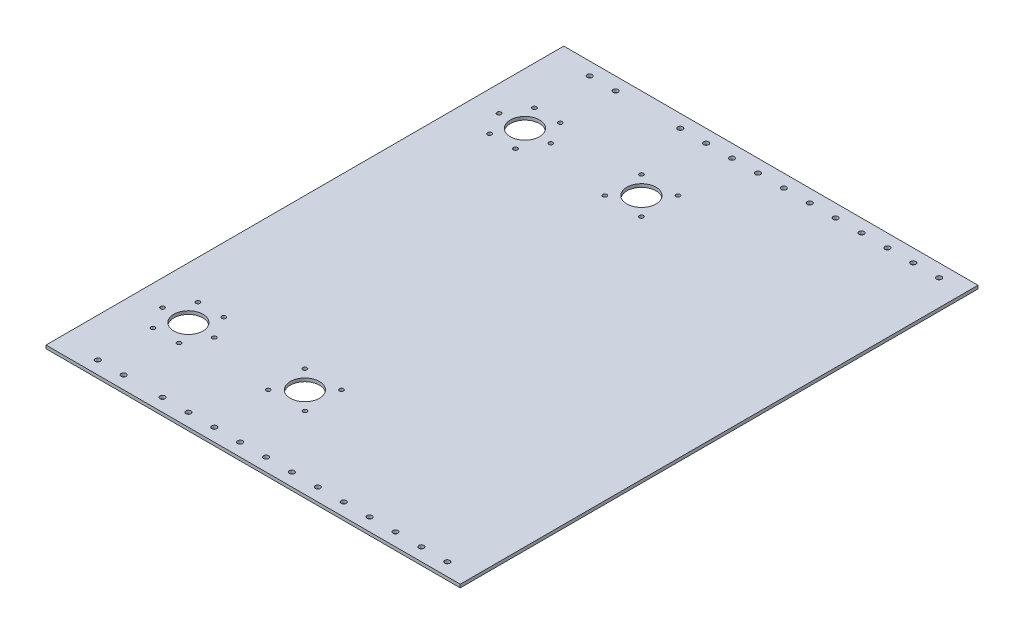
SolidWorks part; units mm, degrees
material "Lexan"
ref_plane "Front Plane" through (0, 0, 0) normal (0, 0, 1) x (1, 0, 0)
ref_plane "Top Plane" through (0, 0, 0) normal (0, 1, 0) x (1, 0, 0)
ref_plane "Right Plane" through (0, 0, 0) normal (1, 0, 0) x (0, 0, -1)
sketch "Sketch1" plane through (0, 0, 0) normal (0, 1, 0) x (1, 0, 0)
  line L1 (0, 0) -> (406.4, 0)
  line L2 (0, 0) -> (0, 508)
  line L3 (0, 508) -> (406.4, 508)
  line L4 (406.4, 0) -> (406.4, 508)
  dimension "D1" = 406.4
  dimension "D2" = 508
extrude "Boss-Extrude1" add sketch "Sketch1" along normal blind 3.175
sketch "Sketch2" plane through (0, 3.175, 0) normal (0, 1, 0) x (1, 0, 0)
  line L0 (107.95, 419.1) -> (107.95, 508) construction
  line L1 (50.8, 419.1) -> (165.1, 419.1) construction
  line L2 (406.4, 0) -> (406.4, 508) construction
  line L3 (50.8, 88.9) -> (165.1, 88.9) construction
  line L5 (406.4, 508) -> (0, 508) construction
  line L6 (107.95, 88.9) -> (107.95, 0) construction
  line L7 (0, 0) -> (406.4, 0) construction
  circle A0 centre (50.8, 419.1) radius 14.2875
  circle A1 centre (165.1, 419.1) radius 14.2875
  circle A2 centre (50.8, 88.9) radius 14.2875
  circle A3 centre (165.1, 88.9) radius 14.2875
  dimension "D1" = 28.575
  dimension "D2" = 28.575
  dimension "D3" = 28.575
  dimension "D4" = 28.575
  dimension "D5" = 114.3
  dimension "D6" = 114.3
  dimension "D7" = 330.2
  dimension "D9" = 241.3
extrude "Cut-Extrude1" cut sketch "Sketch2" against normal blind 3.175
sketch "Sketch3" plane through (0, 3.175, 0) normal (0, 1, 0) x (1, 0, 0)
  line L0 (0, 12.7) -> (406.4, 12.7) construction
  line L1 (0, 508) -> (0, 0) construction
  line L2 (406.4, 0) -> (406.4, 508) construction
  line L3 (0, 0) -> (406.4, 0) construction
  line L4 (101.6, 0) -> (101.6, 12.7) construction
  line L5 (0, 254) -> (406.4, 254) construction
  line L6 (101.6, 508) -> (101.6, 495.3) construction
  line L7 (0, 495.3) -> (406.4, 495.3) construction
  circle A0 centre (38.1, 12.7) radius 2.4892
  circle A1 centre (63.5, 12.7) radius 2.4892
  circle A2 centre (127, 12.7) radius 2.4892
  circle A3 centre (152.4, 12.7) radius 2.4892
  circle A4 centre (177.8, 12.7) radius 2.4892
  circle A5 centre (203.2, 12.7) radius 2.4892
  circle A6 centre (228.6, 12.7) radius 2.4892
  circle A7 centre (254, 12.7) radius 2.4892
  circle A8 centre (279.4, 12.7) radius 2.4892
  circle A9 centre (304.8, 12.7) radius 2.4892
  circle A10 centre (330.2, 12.7) radius 2.4892
  circle A11 centre (355.6, 12.7) radius 2.4892
  circle A12 centre (381, 12.7) radius 2.4892
  circle A13 centre (381, 495.3) radius 2.4892
  circle A14 centre (355.6, 495.3) radius 2.4892
  circle A15 centre (330.2, 495.3) radius 2.4892
  circle A16 centre (304.8, 495.3) radius 2.4892
  circle A17 centre (279.4, 495.3) radius 2.4892
  circle A18 centre (254, 495.3) radius 2.4892
  circle A19 centre (228.6, 495.3) radius 2.4892
  circle A20 centre (203.2, 495.3) radius 2.4892
  circle A21 centre (177.8, 495.3) radius 2.4892
  circle A22 centre (152.4, 495.3) radius 2.4892
  circle A23 centre (127, 495.3) radius 2.4892
  circle A24 centre (63.5, 495.3) radius 2.4892
  circle A25 centre (38.1, 495.3) radius 2.4892
  circle A27 centre (101.6, 12.7) radius 2.4892
  dimension "D1" = 4.9784
  dimension "D2" = 38.1
  dimension "D4" = 25.4
  dimension "D6" = 25.4
  dimension "D7" = 11
  dimension "D3" = 12.7
  dimension "D5" = 38.1
extrude "Cut-Extrude2" cut sketch "Sketch3" against normal through all both and the other way through all
sketch "Sketch4" plane through (0, 3.175, 0) normal (0, 1, 0) x (1, 0, 0)
  line L0 (25.4, 419.1) -> (38.1, 441.097) construction
  line L1 (38.1, 441.097) -> (63.5, 441.097) construction
  line L2 (63.5, 441.097) -> (76.2, 419.1) construction
  line L3 (76.2, 419.1) -> (63.5, 397.103) construction
  line L4 (63.5, 397.103) -> (38.1, 397.103) construction
  line L5 (38.1, 397.103) -> (25.4, 419.1) construction
  line L6 (0, 254) -> (406.4, 254) construction
  line L7 (183.0605, 401.1395) -> (147.1395, 401.1395) construction
  line L8 (183.0605, 401.1395) -> (183.0605, 437.0605) construction
  line L9 (183.0605, 437.0605) -> (147.1395, 437.0605) construction
  line L10 (147.1395, 401.1395) -> (147.1395, 437.0605) construction
  line L11 (183.0605, 401.1395) -> (147.1395, 437.0605) construction
  line L12 (183.0605, 437.0605) -> (147.1395, 401.1395) construction
  line L13 (0, 508) -> (0, 0) construction
  line L14 (406.4, 0) -> (406.4, 508) construction
  line L15 (183.0605, 70.9395) -> (147.1395, 106.8605) construction
  line L16 (183.0605, 106.8605) -> (147.1395, 70.9395) construction
  line L17 (147.1395, 106.8605) -> (147.1395, 70.9395) construction
  line L18 (183.0605, 70.9395) -> (147.1395, 70.9395) construction
  line L19 (183.0605, 106.8605) -> (183.0605, 70.9395) construction
  line L20 (183.0605, 106.8605) -> (147.1395, 106.8605) construction
  line L21 (38.1, 110.897) -> (25.4, 88.9) construction
  line L22 (63.5, 110.897) -> (38.1, 110.897) construction
  line L23 (76.2, 88.9) -> (63.5, 110.897) construction
  line L24 (63.5, 66.903) -> (76.2, 88.9) construction
  line L25 (38.1, 66.903) -> (63.5, 66.903) construction
  line L26 (25.4, 88.9) -> (38.1, 66.903) construction
  circle A0 centre (50.8, 419.1) radius 25.4 construction
  circle A1 centre (76.2, 419.1) radius 2.0193
  circle A2 centre (25.4, 419.1) radius 2.0193
  circle A3 centre (38.1, 441.097) radius 2.0193
  circle A4 centre (63.5, 441.097) radius 2.0193
  circle A5 centre (63.5, 397.103) radius 2.0193
  circle A6 centre (38.1, 397.103) radius 2.0193
  circle A7 centre (147.1395, 437.0605) radius 2.0193
  circle A8 centre (183.0605, 437.0605) radius 2.0193
  circle A9 centre (183.0605, 401.1395) radius 2.0193
  circle A10 centre (147.1395, 401.1395) radius 2.0193
  circle A11 centre (50.8, 88.9) radius 25.4 construction
  circle A12 centre (147.1395, 106.8605) radius 2.0193
  circle A13 centre (183.0605, 106.8605) radius 2.0193
  circle A14 centre (183.0605, 70.9395) radius 2.0193
  circle A15 centre (147.1395, 70.9395) radius 2.0193
  circle A16 centre (38.1, 110.897) radius 2.0193
  circle A17 centre (63.5, 110.897) radius 2.0193
  circle A18 centre (63.5, 66.903) radius 2.0193
  circle A19 centre (38.1, 66.903) radius 2.0193
  circle A20 centre (25.4, 88.9) radius 2.0193
  circle A21 centre (76.2, 88.9) radius 2.0193
  point P15 (165.1, 419.1)
  point P53 (165.1, 88.9)
  dimension "D1" = 50.8
  dimension "D2" = 4.0386
  dimension "D5" = 4.0386
  dimension "D3" = 35.921
  dimension "D4" = 35.921
extrude "Cut-Extrude3" cut sketch "Sketch4" against normal through all both and the other way through all
